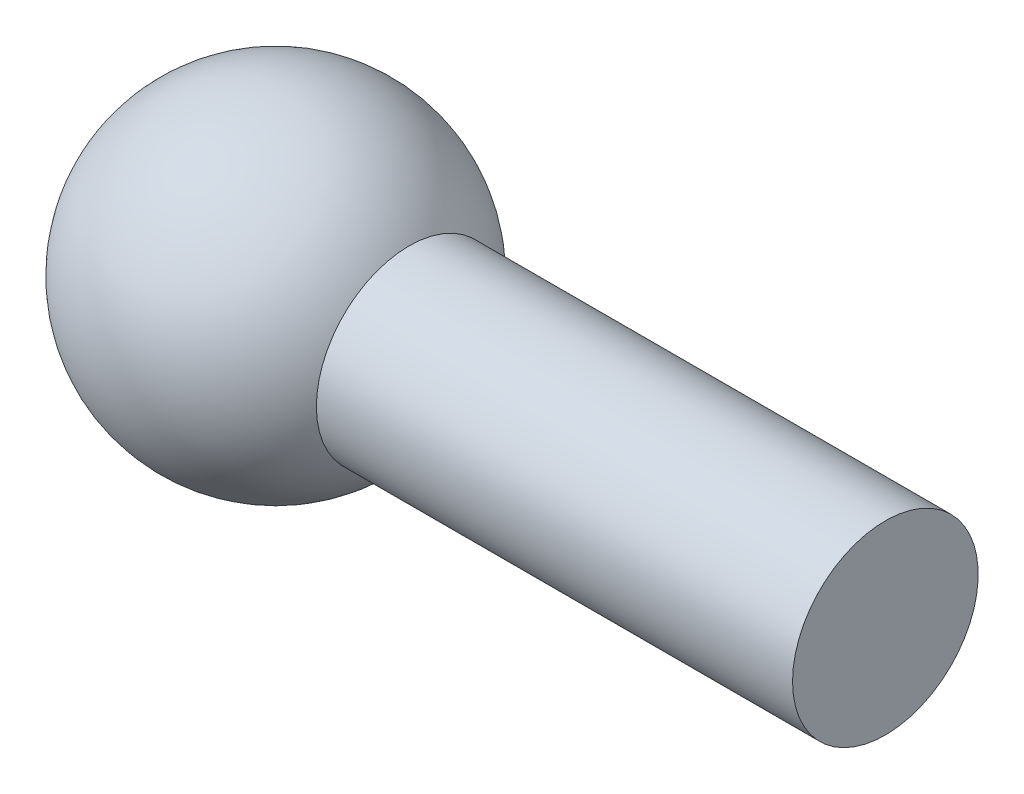
SolidWorks part; units mm, degrees
ref_plane "Front Plane" through (0, 0, 0) normal (0, 0, 1) x (1, 0, 0)
ref_plane "Top Plane" through (0, 0, 0) normal (0, 1, 0) x (1, 0, 0)
ref_plane "Right Plane" through (0, 0, 0) normal (1, 0, 0) x (0, 0, -1)
sketch "Sketch2" plane through (0, 0, 0) normal (0, 0, 1) x (1, 0, 0)
  line L0 (-10, 0) -> (10, 0) construction
  arc A0 (10, 0) -> (-10, 0) centre (0, 0) ccw
  dimension "D1" = 20
revolve "Revolve-Thin1" add sketch "Sketch2" angle 360 about L0
sketch "Sketch3" plane through (0, 0, 0) normal (0, 0, 1) x (1, 0, 0)
  line L0 (15, 0) -> (15, 11.4176)
  line L1 (15, 11.4176) -> (75, 11.4176)
  line L2 (75, 11.4176) -> (75, 0)
  line L3 (15, 0) -> (75, 0) construction
  dimension "D1" = 15
  dimension "D2" = 60
  dimension "D3" = 11.4176
revolve "Revolve-Thin2" add sketch "Sketch3" angle 360 about L3
